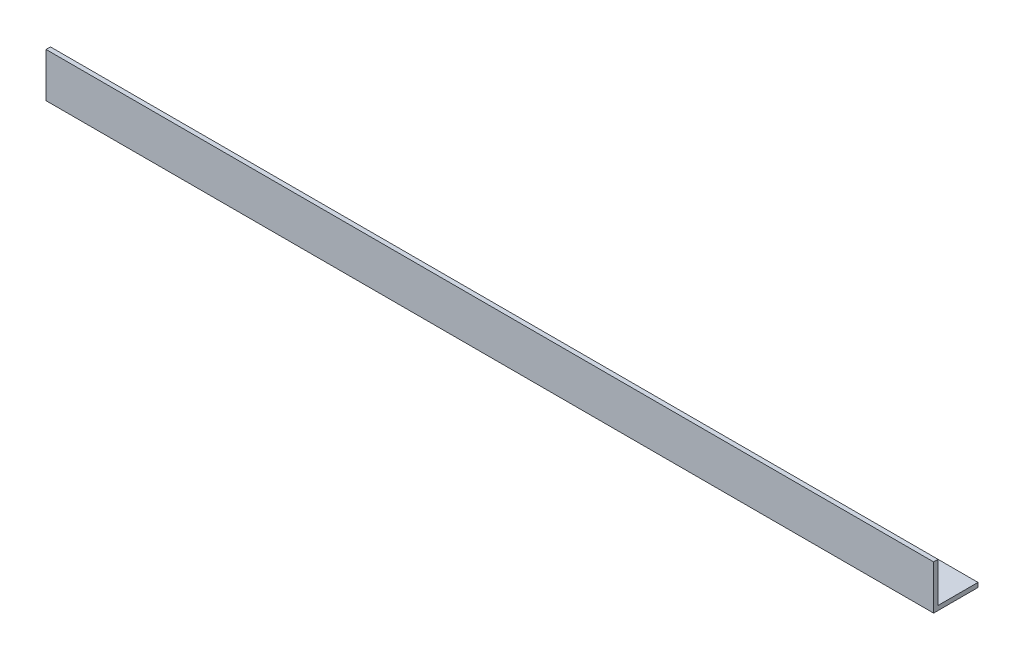
SolidWorks part; units mm, degrees
ref_plane "Спереди" through (0, 0, 0) normal (0, 0, 1) x (1, 0, 0)
ref_plane "Сверху" through (0, 0, 0) normal (0, 1, 0) x (1, 0, 0)
ref_plane "Справа" through (0, 0, 0) normal (1, 0, 0) x (0, 0, -1)
sketch "Эскиз1" plane through (0, 0, 0) normal (1, 0, 0) x (0, 0, -1)
  line L0 (0, 0) -> (0, 15)
  line L1 (0, 15) -> (1.5, 15)
  line L2 (1.5, 15) -> (1.5, 1.5)
  line L3 (1.5, 1.5) -> (15, 1.5)
  line L4 (15, 1.5) -> (15, 0)
  line L5 (15, 0) -> (0, 0)
  dimension "D1" = 15
  dimension "D2" = 15
  dimension "D3" = 1.5
  dimension "D4" = 1.5
extrude "Бобышка-Вытянуть1" add sketch "Эскиз1" along normal blind 300
